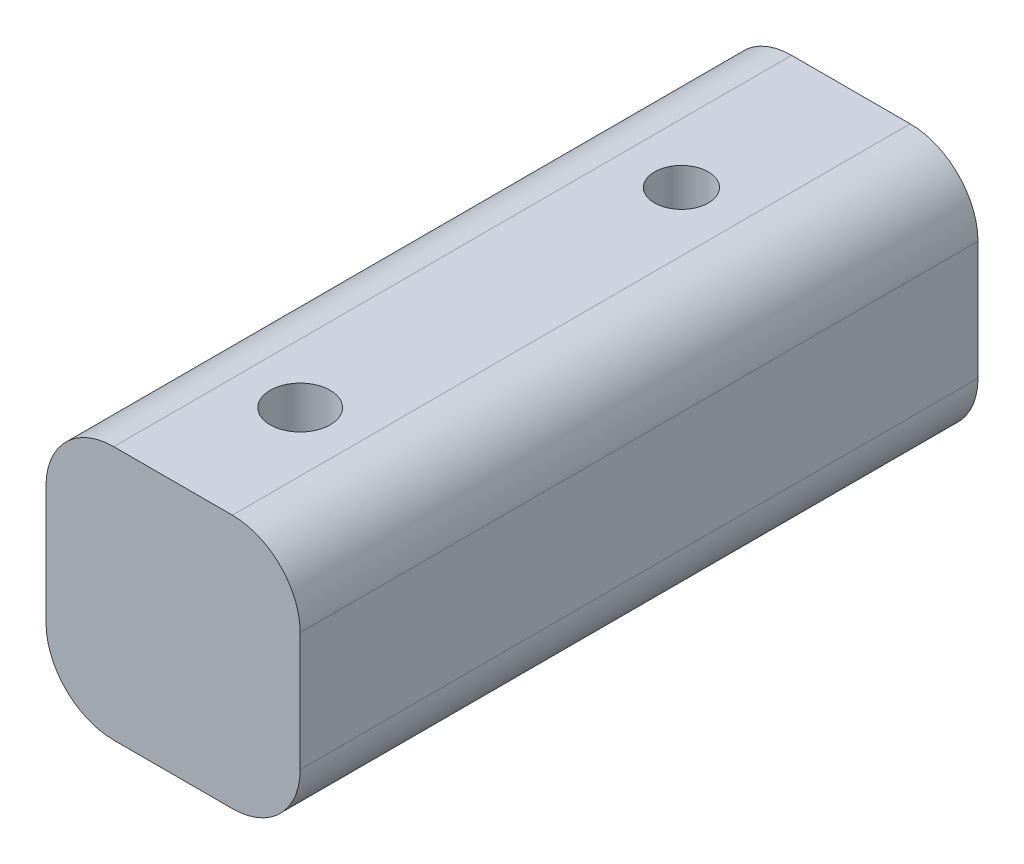
SolidWorks part; units mm, degrees
material "AISI 304"
ref_plane "Front Plane" through (0, 0, 0) normal (0, 0, 1) x (1, 0, 0)
ref_plane "Top Plane" through (0, 0, 0) normal (0, 1, 0) x (1, 0, 0)
ref_plane "Right Plane" through (0, 0, 0) normal (1, 0, 0) x (0, 0, -1)
sketch "Sketch1" plane through (0, 0, 0) normal (0, 0, 1) x (1, 0, 0)
  line L1 (-9.525, 9.525) -> (9.525, 9.525)
  line L2 (-9.525, 9.525) -> (-9.525, -9.525)
  line L3 (-9.525, -9.525) -> (9.525, -9.525)
  line L4 (9.525, 9.525) -> (9.525, -9.525)
  line L5 (-9.525, 9.525) -> (9.525, -9.525) construction
  line L6 (-9.525, -9.525) -> (9.525, 9.525) construction
  point P0 (0, 0)
  dimension "D1" = 19.05
  dimension "D2" = 19.05
extrude "Boss-Extrude1" add sketch "Sketch1" along normal blind 50.8
sketch "Sketch2" plane through (0, -9.525, 0) normal (0, -1, 0) x (1, 0, 0)
  line L3 (-0.7938, 47.625) -> (0.7938, 47.625)
  line L4 (-3.9688, 44.45) -> (-3.9688, 38.1)
  line L5 (-0.7938, 34.925) -> (0.7938, 34.925)
  line L6 (3.9688, 44.45) -> (3.9688, 38.1)
  line L7 (-3.9688, 47.625) -> (3.9688, 34.925) construction
  line L8 (-3.9688, 34.925) -> (3.9688, 47.625) construction
  line L10 (-9.525, 50.8) -> (9.525, 50.8) construction
  circle A2 centre (0, 41.275) radius 6.35
  arc A3 (-3.9688, 38.1) -> (-0.7938, 34.925) centre (-0.7938, 38.1) ccw
  arc A4 (0.7938, 34.925) -> (3.9688, 38.1) centre (0.7938, 38.1) ccw
  arc A5 (3.9688, 44.45) -> (0.7938, 47.625) centre (0.7938, 44.45) ccw
  arc A6 (-0.7938, 47.625) -> (-3.9688, 44.45) centre (-0.7938, 44.45) ccw
  dimension "D2" = 12.7
  dimension "D1" = 3.175
  dimension "D3" = 7.9375
  dimension "D4" = 9.525
extrude "Cut-Extrude1" cut sketch "Sketch2" against normal blind 12.7 contours L4 A3 L5 A4 L6 A5 L3 A6
hole_wizard "#8 Clearance Hole1" positions "Sketch3" profile "Sketch4" hole size "#8" standard "ANSI Inch" end condition through all
sketch "Sketch3" plane through (0, 3.175, 0) normal (0, -1, 0) x (-1, 0, 0)
  line L0 (-3.9688, -41.275) -> (3.9688, -41.275)
  line L1 (-3.9688, -44.45) -> (-3.9688, -38.1) construction
  line L2 (3.9688, -44.45) -> (3.9688, -38.1) construction
  point P0 (0, -41.275)
sketch "Sketch4" plane through (0, 3.175, 41.275) normal (1, 0, 0) x (0, 0, -1)
  line L0 (0, 0) -> (0, 6.35)
  line L1 (0, 6.35) -> (2.2479, 6.35)
  line L2 (2.2479, 6.35) -> (2.2479, 0)
  line L5 (2.2479, 0) -> (0, 0)
  line L11 (0, -6.35) -> (0, 107.95) construction
  dimension "Thru Hole Dia." = 4.4958
  dimension "Thru Hole Depth" = 6.35
fillet "Fillet1" radius 0.381 8 edges at (-3.0388, -9.525, 46.6951) (0, -9.525, 47.625) (3.0388, -9.525, 46.6951) (3.9688, -9.525, 41.275) (3.0388, -9.525, 35.8549) (0, -9.525, 34.925) (-3.0388, -9.525, 35.8549) (-3.9688, -9.525, 41.275)
hole_wizard "#10-32 Tapped Hole1" positions "Sketch5" profile "Sketch6" tap size "#10-32" standard "ANSI Inch" end condition through all
sketch "Sketch5" plane through (0, 9.525, 0) normal (0, 1, 0) x (1, 0, 0)
  line L0 (9.525, 0) -> (-9.525, 0) construction
  point P0 (0, -12.7)
  point P5 (0, 0)
  dimension "D1" = 12.7
cosmetic thread "Hole Thread1" parameters "D2"=4.826
sketch "Sketch6" plane through (0, 9.525, 12.7) normal (1, 0, 0) x (0, 0, 1)
  line L0 (0, 0) -> (0, 19.05)
  line L1 (0, 19.05) -> (2.0193, 19.05)
  line L2 (2.0193, 19.05) -> (2.0193, 0)
  line L5 (2.0193, 0) -> (0, 0)
  line L11 (0, -6.35) -> (0, 107.95) construction
  dimension "Thru Tap Drill Dia." = 4.0386
  dimension "Thru Tap Drill Depth" = 19.05
fillet "Fillet2" radius 5.08 4 edges at (-9.525, -9.525, 25.4) (9.525, -9.525, 25.4) (9.525, 9.525, 25.4) (-9.525, 9.525, 25.4)
